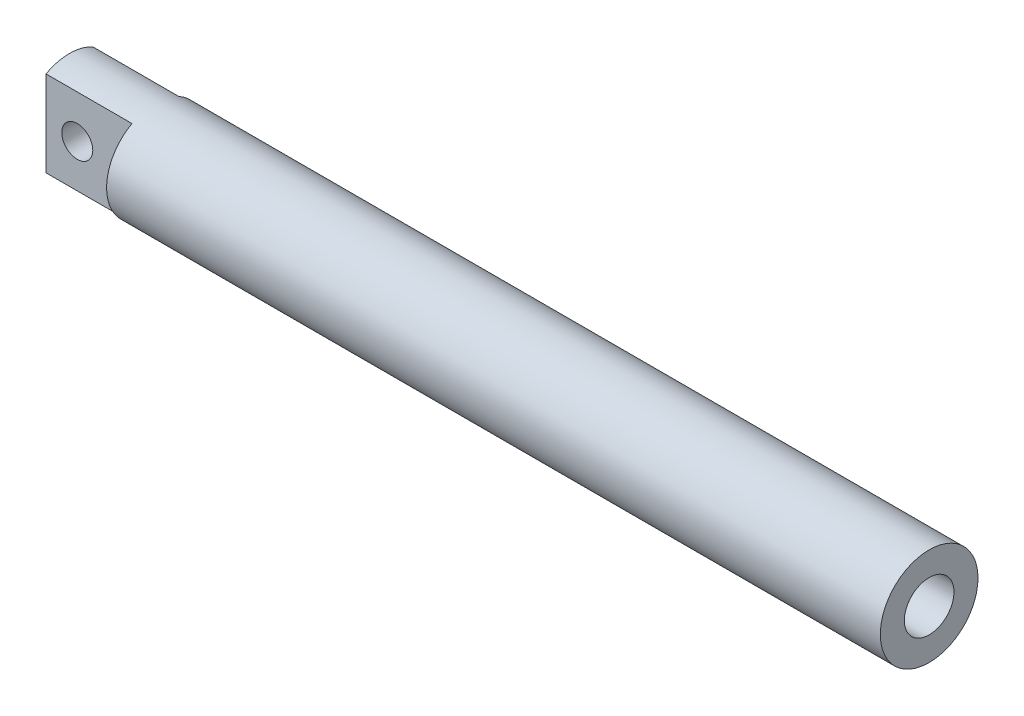
SolidWorks part; units mm, degrees
ref_plane "Alzado" through (0, 0, 0) normal (0, 0, 1) x (1, 0, 0)
ref_plane "Planta" through (0, 0, 0) normal (0, 1, 0) x (1, 0, 0)
ref_plane "Vista lateral" through (0, 0, 0) normal (1, 0, 0) x (0, 0, -1)
sketch "Croquis1" plane through (0, 0, 0) normal (1, 0, 0) x (0, 0, -1)
  circle A0 centre (0, 0) radius 12.5
  dimension "D1" = 25
extrude "Saliente-Extruir1" add sketch "Croquis1" along normal blind 220
sketch "Croquis2" plane through (0, 0, 0) normal (-1, 0, 0) x (0, 0, 1)
  line L0 (0, 12.5) -> (0, 0) construction
  line L2 (-13.8425, 14.641) -> (-6, 14.641)
  line L3 (-13.8425, 14.641) -> (-13.8425, -13.8626)
  line L4 (-13.8425, -13.8626) -> (-6, -13.8626)
  line L5 (-6, 14.641) -> (-6, -13.8626)
  line L6 (13.5638, -13.8626) -> (6, -13.8626)
  line L7 (13.5638, -13.8626) -> (13.5638, 15.4372)
  line L8 (13.5638, 15.4372) -> (6, 15.4372)
  line L9 (6, -13.8626) -> (6, 15.4372)
  circle A0 centre (0, 0) radius 12.5 construction
  dimension "D1" = 6
  dimension "D2" = 6
extrude "Cortar-Extruir1" cut sketch "Croquis2" against normal blind 22
sketch "Croquis3" plane through (0, 0, 6) normal (0, 0, 1) x (1, 0, 0)
  line L0 (0, 0) -> (22, 0) construction
  line L1 (22, 10.9659) -> (22, -10.9659) construction
  line L2 (0, -10.9659) -> (0, 10.9659) construction
  circle A0 centre (8, 0) radius 3.9688
  dimension "D1" = 7.9375
  dimension "D2" = 8
extrude "Cortar-Extruir2" cut sketch "Croquis3" against normal blind 22
sketch "Croquis4" plane through (220, 0, 0) normal (1, 0, 0) x (0, 0, -1)
  circle A0 centre (0, 0) radius 6.35
  dimension "D1" = 12.7
extrude "Cortar-Extruir3" cut sketch "Croquis4" against normal blind 140
